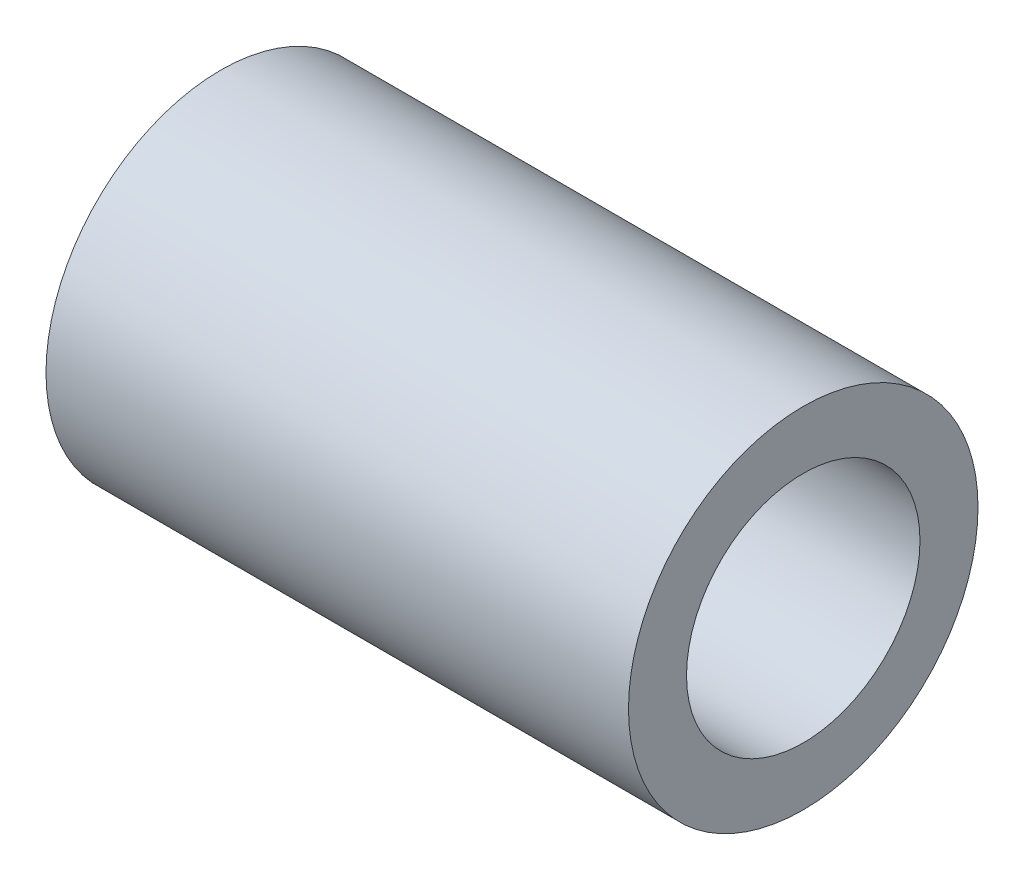
SolidWorks part; units mm, degrees
ref_plane "Front" through (0, 0, 0) normal (0, 0, 1) x (1, 0, 0)
ref_plane "Top" through (0, 0, 0) normal (0, 1, 0) x (1, 0, 0)
ref_plane "Right" through (0, 0, 0) normal (1, 0, 0) x (0, 0, -1)
sketch "Sketch1" plane through (0, 0, 0) normal (0, 0, 1) x (1, 0, 0)
  line L0 (0, 0) -> (66.4064, 0) construction
  line L2 (0, 9.525) -> (31.75, 9.525)
  line L3 (0, 9.525) -> (0, 6.3627)
  line L4 (0, 6.3627) -> (31.75, 6.3627)
  line L5 (31.75, 9.525) -> (31.75, 6.3627)
  dimension "D1" = 12.7254
  dimension "D2" = 19.05
  dimension "D3" = 31.75
revolve "Revolve1" add sketch "Sketch1" angle 360 about L0
